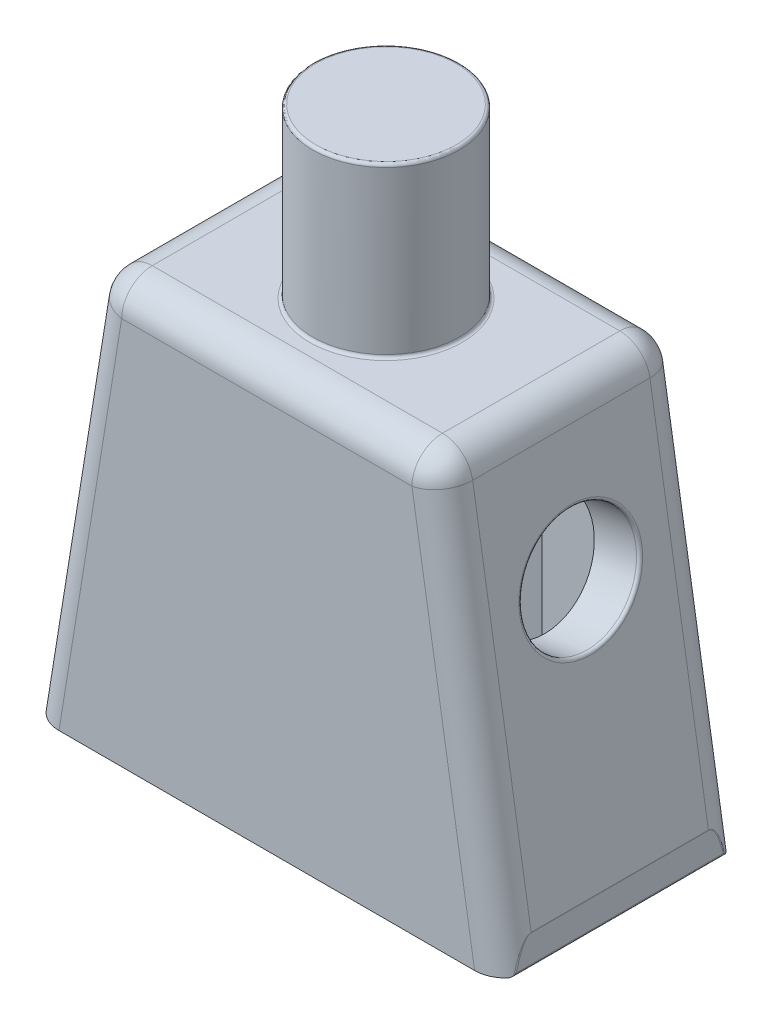
SolidWorks part; units mm, degrees
ref_plane "Alzado" through (0, 0, 0) normal (0, 0, 1) x (1, 0, 0)
ref_plane "Planta" through (0, 0, 0) normal (0, 1, 0) x (1, 0, 0)
ref_plane "Vista lateral" through (0, 0, 0) normal (1, 0, 0) x (0, 0, -1)
sketch "Croquis1" plane through (0, 0, 0) normal (0, 0, 1) x (1, 0, 0)
  line L0 (7.65, 0) -> (-7.65, 0)
  line L1 (-7.65, 0) -> (-7.65, 1)
  line L2 (-7.65, 1) -> (-5.6, 13.7)
  line L3 (-5.6, 13.7) -> (5.6, 13.7)
  line L4 (5.6, 13.7) -> (7.65, 1)
  line L5 (7.65, 1) -> (7.65, 0)
  line L6 (0, 0) -> (0, 10.9724) construction
  dimension "D1" = 15.3
  dimension "D2" = 1
  dimension "D3" = 11.2
  dimension "D4" = 12.7
extrude "Saliente-Extruir1" add sketch "Croquis1" along normal mid plane 7.8
shell "Vaciado1" thickness 1.5
sketch "Croquis2" plane through (7.6131, 1.2289, 0) normal (0.9872, 0.1594, 0) x (0, 0, -1)
  line L0 (-3.9, -1.2191) -> (3.9, -1.2191) construction
  circle A0 centre (0, 7.7809) radius 1.9
  point P5 (0, 0)
  dimension "D1" = 3.8
  dimension "D2" = 9
extrude "Cortar-Extruir1" cut sketch "Croquis2" against normal up to next (1.5 mm away)
mirror "Simetría1" about plane through (0, 0, 0) normal (1, 0, 0) of "Cortar-Extruir1"
sketch "Croquis3" plane through (0, 0, 0) normal (0, -1, 0) x (1, 0, 0)
  line L0 (0, 0) -> (0, 6.5225) construction
  line L1 (1.5, 2.4) -> (1.5, 1.6)
  line L2 (4.3227, 2.4) -> (-4.3227, 2.4) construction
  line L3 (1.5, 1.6) -> (2.7, 2.4)
  line L4 (1.5, 2.4) -> (2.7, 2.4)
  line L5 (-1.5, 1.6) -> (-2.7, 2.4)
  line L6 (-1.5, 2.4) -> (-2.7, 2.4)
  line L7 (-1.5, 2.4) -> (-1.5, 1.6)
  dimension "D1" = 0.8
  dimension "D2" = 1.5
  dimension "D3" = 1.2
extrude "Saliente-Extruir2" add sketch "Croquis3" against normal up to next (12.2 mm away)
mirror "Simetría2" about plane through (0, 0, 0) normal (0, 0, 1) of "Saliente-Extruir2"
sketch "Croquis4" plane through (0, 13.7, 0) normal (0, 1, 0) x (1, 0, 0)
  circle A0 centre (0, 0) radius 2.4
  dimension "D1" = 4.8
extrude "Saliente-Extruir3" add sketch "Croquis4" along normal blind 5.5
sketch "Croquis5" plane through (0, 12.2, 0) normal (0, -1, 0) x (1, 0, 0)
  circle A0 centre (0, 0) radius 1.25
  dimension "D1" = 2.5
extrude "Cortar-Extruir2" cut sketch "Croquis5" against normal blind 4.25
fillet "Redondeo1" radius 1 8 edges at (6.625, 7.35, -3.9) (-6.625, 7.35, -3.9) (-6.625, 7.35, 3.9) (6.625, 7.35, 3.9) (5.6, 13.7, 0) (0, 13.7, -3.9) (0, 13.7, 3.9) (-5.6, 13.7, 0)
fillet "Redondeo2" radius 0.1 12 edges at (-7.65, 0.7448, 3.1823) (-7.65, 0, 0) (-7.65, 0.7448, -3.1823) (-7.65, 1, 0) (7.65, 0.7448, 3.1823) (7.65, 1, 0) (7.65, 0.7448, -3.1823) (7.65, 0, 0) (0, 13.7, 2.4) (0, 19.2, 2.4) (-6.0704, 10.7861, 0) (6.0704, 10.7861, 0)
